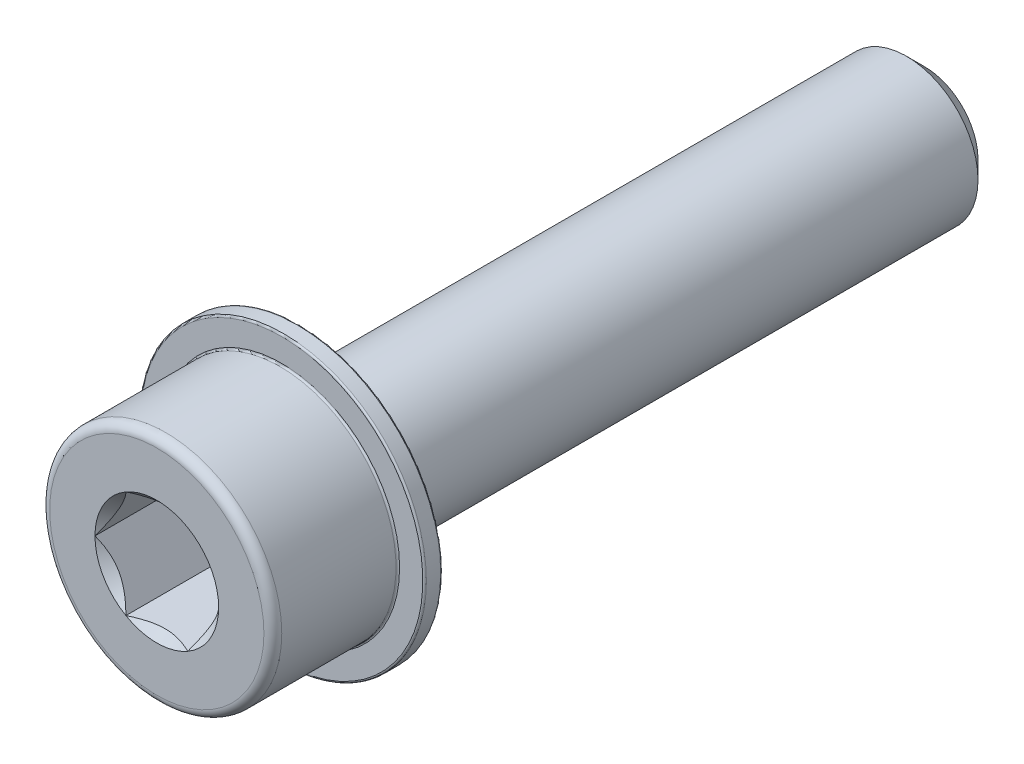
SolidWorks part; units mm, degrees
material "Acciaio inossidabile (ferroso)"
ref_plane "Piano frontale" through (0, 0, 0) normal (0, 0, 1) x (1, 0, 0)
ref_plane "Piano superiore" through (0, 0, 0) normal (0, 1, 0) x (1, 0, 0)
ref_plane "Piano destro" through (0, 0, 0) normal (1, 0, 0) x (0, 0, -1)
sketch "Schizzo1" plane through (0, 0, 0) normal (0, 0, 1) x (1, 0, 0)
  circle A0 centre (0, 0) radius 4
  dimension "D1" = 8
extrude "Estrusione-Estrusione1" add sketch "Schizzo1" along normal blind 35
cosmetic thread "Filettatura cosmetica2" parameters "D2"=6.619
chamfer "Smusso1" distance 1 angle 45 1 edges at (4, 0, 0)
sketch "Schizzo6" plane through (0, 0, 35) normal (0, 0, 1) x (1, 0, 0)
  circle A0 centre (0, 0) radius 6.5
  dimension "D1" = 13
extrude "Estrusione-Estrusione3" add sketch "Schizzo6" along normal blind 8
sketch "Schizzo7" plane through (0, 0, 43) normal (0, 0, 1) x (1, 0, 0)
  line L1 (1.7321, 3) -> (-1.7321, 3)
  line L2 (-1.7321, 3) -> (-3.4641, 0)
  line L3 (-3.4641, 0) -> (-1.7321, -3)
  line L4 (-1.7321, -3) -> (1.7321, -3)
  line L5 (1.7321, -3) -> (3.4641, 0)
  line L6 (3.4641, 0) -> (1.7321, 3)
  circle A1 centre (0, 0) radius 3 construction
  dimension "D1" = 6
extrude "Taglio-Estrusione3" cut sketch "Schizzo7" against normal blind 6
sketch "Schizzo8" plane through (0, 0, 43) normal (0, 0, 1) x (1, 0, 0)
  circle A0 centre (0, 0) radius 3.4641
extrude "Taglio-Estrusione4" cut sketch "Schizzo8" against normal blind 1 draft 45
fillet "Raccordo1" radius 0.5 1 edges at (6.5, 0, 43)
sketch "Schizzo9" plane through (0, 0, 35) normal (0, 0, -1) x (-1, 0, 0)
  circle A0 centre (0, 0) radius 6.5
  circle A1 centre (0, 0) radius 8
  dimension "D1" = 13
  dimension "D2" = 16
extrude "Estrusione-Estrusione4" add sketch "Schizzo9" against normal blind 1
fillet "Raccordo2" radius 0.1 3 edges at (-8, 0, 36) (-6.5, 0, 36) (-8, 0, 35)
